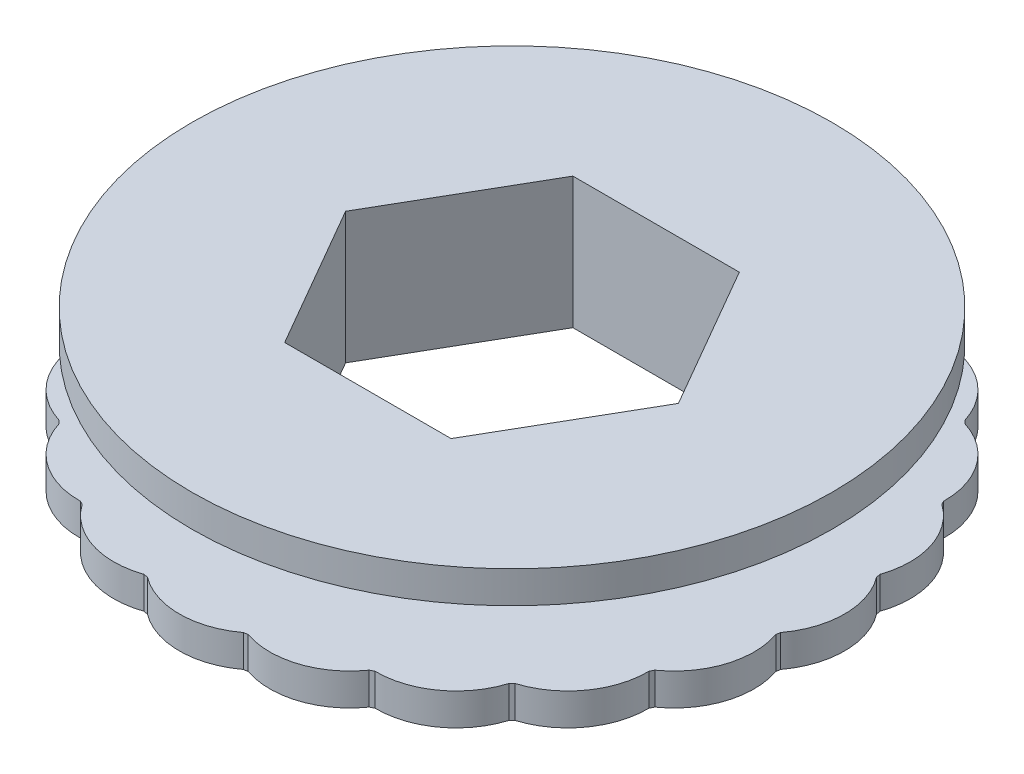
SolidWorks part; units mm, degrees
ref_plane "Front Plane" through (0, 0, 0) normal (0, 0, 1) x (1, 0, 0)
ref_plane "Top Plane" through (0, 0, 0) normal (0, 1, 0) x (1, 0, 0)
ref_plane "Right Plane" through (0, 0, 0) normal (1, 0, 0) x (0, 0, -1)
sketch "Sketch1" plane through (0, 0, 0) normal (1, 0, 0) x (0, 0, -1)
  line L1 (-3.5, 0.525) -> (0, 0.525) construction
  line L2 (-3.5, 0.525) -> (-3.5, -0.525)
  line L3 (-3.5, -0.525) -> (0, -0.525) construction
  line L4 (0, 0.525) -> (0, -0.525)
  line L5 (-5, 0.525) -> (-3.5, 0.525)
  line L6 (-5, 0.525) -> (-5, 1.025)
  line L7 (-5, 1.025) -> (0, 1.025)
  line L8 (0, 0.525) -> (0, 1.025)
  line L9 (-5, -0.525) -> (-3.5, -0.525)
  line L10 (-5, -0.525) -> (-5, -1.025)
  line L11 (-5, -1.025) -> (0, -1.025)
  line L12 (0, -0.525) -> (0, -1.025)
  line L13 (0, 0) -> (0, -2.8832) construction
  line L14 (-3.5, 0.525) -> (0, 0.525) construction
  line L15 (-3.5, -0.525) -> (0, -0.525) construction
  dimension "D1" = 0.5
  dimension "D2" = 1.05
  dimension "D4" = 10
  dimension "D5" = 7
  dimension "D6" = 1.5
revolve "Revolve1" add sketch "Sketch1" angle 360 about L13
sketch "Sketch3" plane through (0, -1.025, 0) normal (0, -1, 0) x (1, 0, 0)
  arc A0 (-0.75, 4.9434) -> (0.75, 4.9434) centre (0, 3.9434) cw
  arc A1 (-0.75, 4.9434) -> (0.75, 4.9434) centre (0, 0) ccw construction
  circle A3 centre (0, 0) radius 5
  arc A4 (0.75, 4.9434) -> (-0.75, 4.9434) centre (0, 0) ccw
  point P10 (0, 5.1934)
  dimension "D2" = 1.5
  dimension "D3" = 0.25
  dimension "D1" = 0
extrude "Boss-Extrude1" add sketch "Sketch3" against normal up to surface (0.5 mm away) up to face at (0, -0.525, 5)
pattern_circular "CirPattern3" count 20 over 360 about axis through (0, 0, 0) along (0, 1, 0) of "Boss-Extrude1"
sketch "Sketch4" plane through (0, 1.025, 0) normal (0, 1, 0) x (1, 0, 0)
  line L1 (1.299, 2.25) -> (-1.299, 2.25)
  line L2 (-1.299, 2.25) -> (-2.5981, 0)
  line L3 (-2.5981, 0) -> (-1.299, -2.25)
  line L4 (-1.299, -2.25) -> (1.299, -2.25)
  line L5 (1.299, -2.25) -> (2.5981, 0)
  line L6 (2.5981, 0) -> (1.299, 2.25)
  circle A0 centre (0, 0) radius 2.25 construction
  dimension "D1" = 4.5
extrude "Cut-Extrude1" cut sketch "Sketch4" against normal through all both and the other way through all
